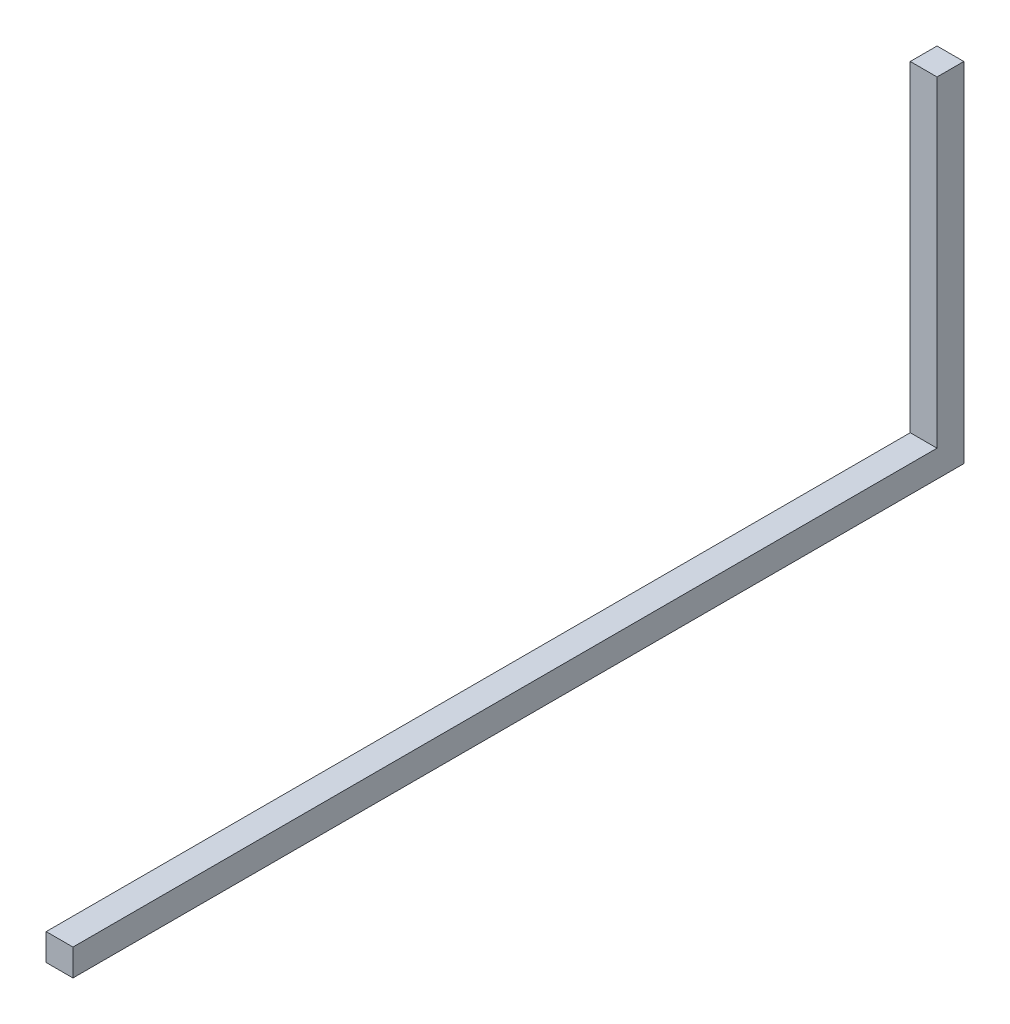
SolidWorks part; units mm, degrees
material "1060-O (SS)"
ref_plane "Front" through (0, 0, 0) normal (0, 0, 1) x (1, 0, 0)
ref_plane "Top" through (0, 0, 0) normal (0, 1, 0) x (1, 0, 0)
ref_plane "Right" through (0, 0, 0) normal (1, 0, 0) x (0, 0, -1)
sketch3d "Трехмерный эскиз2"
  line L0 (0, 0, 0) -> (0, 0, -13.1)
  line L1 (0, 0, -13.1) -> (0, 5, -13.1)
sketch "Эскиз4" plane through (0, 0, 0) normal (0, 0, 1) x (1, 0, 0)
  line L1 (-0.2, -0.2) -> (0.2, -0.2)
  line L2 (-0.2, -0.2) -> (-0.2, 0.2)
  line L3 (-0.2, 0.2) -> (0.2, 0.2)
  line L4 (0.2, -0.2) -> (0.2, 0.2)
sweep "По траектории1" add profiles "Эскиз4" path "Трехмерный эскиз2"
